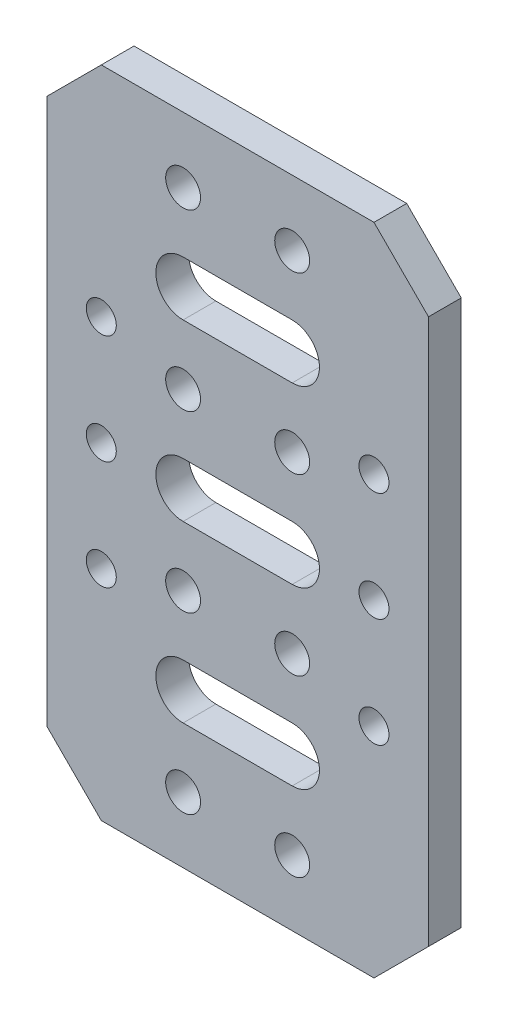
SolidWorks part; units mm, degrees
material "Thornel Mat VMA"
ref_plane "前视基准面" through (0, 0, 0) normal (0, 0, 1) x (1, 0, 0)
ref_plane "上视基准面" through (0, 0, 0) normal (0, 1, 0) x (1, 0, 0)
ref_plane "右视基准面" through (0, 0, 0) normal (1, 0, 0) x (0, 0, -1)
sketch "草图1" plane through (0, 0, 0) normal (0, 0, 1) x (1, 0, 0)
  line L0 (0, 0) -> (-5, 0) construction
  line L1 (-17.5, 30) -> (17.5, 30)
  line L2 (-17.5, 30) -> (-17.5, -30)
  line L3 (-17.5, -30) -> (17.5, -30)
  line L4 (17.5, 30) -> (17.5, -30)
  line L5 (-17.5, 30) -> (17.5, -30) construction
  line L6 (-17.5, -30) -> (17.5, 30) construction
  line L7 (-5, 0) -> (-5, 8) construction
  line L8 (0, 0) -> (0, 6.0639) construction
  circle A0 centre (-5, 8) radius 1.6
  circle A1 centre (5, 8) radius 1.6
  circle A2 centre (-5, 24) radius 1.6
  circle A3 centre (5, 24) radius 1.6
  circle A4 centre (-5, -8) radius 1.6
  circle A5 centre (5, -8) radius 1.6
  circle A6 centre (-5, -24) radius 1.6
  circle A7 centre (5, -24) radius 1.6
  point P0 (0, 0)
  dimension "D5" = 3.2
  dimension "D1" = 35
  dimension "D2" = 60
  dimension "D3" = 5
  dimension "D4" = 8
  dimension "D6" = 2
  dimension "D7" = 3
extrude "凸台-拉伸1" add sketch "草图1" along normal blind 3
sketch "草图2" plane through (0, 0, 3) normal (0, 0, 1) x (1, 0, 0)
  line L0 (0, 0) -> (12.5, 0) construction
  line L1 (0, 0) -> (0, -14.4385) construction
  circle A0 centre (12.5, 0) radius 1.375
  circle A1 centre (-12.5, 0) radius 1.375
  circle A2 centre (-12.5, 10) radius 1.375
  circle A3 centre (12.5, 10) radius 1.375
  circle A4 centre (-12.5, -10) radius 1.375
  circle A5 centre (12.5, -10) radius 1.375
  dimension "D2" = 2.75
  dimension "D1" = 12.5
  dimension "D3" = 2
  dimension "D4" = 2
extrude "切除-拉伸1" cut sketch "草图2" against normal up to next
chamfer "倒角1" distance 5 angle 45 4 edges at (17.5, -30, 1.5) (-17.5, -30, 1.5) (17.5, 30, 1.5) (-17.5, 30, 1.5)
sketch "草图3" plane through (0, 0, 3) normal (0, 0, 1) x (1, 0, 0)
  line L0 (-5, 0) -> (5, 0) construction
  line L1 (-5, 2.5) -> (5, 2.5)
  line L2 (-5, -2.5) -> (5, -2.5)
  line L3 (-5, 16) -> (5, 16) construction
  line L4 (-5, 18.5) -> (5, 18.5)
  line L5 (-5, 13.5) -> (5, 13.5)
  line L6 (-5, 0) -> (5, 0) construction
  line L7 (-5, 2.5) -> (5, 2.5)
  line L8 (-5, -2.5) -> (5, -2.5)
  line L9 (-5, -16) -> (5, -16) construction
  line L10 (-5, -13.5) -> (5, -13.5)
  line L11 (-5, -18.5) -> (5, -18.5)
  arc A0 (-5, 2.5) -> (-5, -2.5) centre (-5, 0) ccw
  arc A1 (5, -2.5) -> (5, 2.5) centre (5, 0) ccw
  arc A2 (-5, 18.5) -> (-5, 13.5) centre (-5, 16) ccw
  arc A3 (5, 13.5) -> (5, 18.5) centre (5, 16) ccw
  arc A4 (-5, 2.5) -> (-5, -2.5) centre (-5, 0) ccw
  arc A5 (5, -2.5) -> (5, 2.5) centre (5, 0) ccw
  arc A6 (-5, -13.5) -> (-5, -18.5) centre (-5, -16) ccw
  arc A7 (5, -18.5) -> (5, -13.5) centre (5, -16) ccw
  point P2 (0, 0)
  point P13 (0, 16)
  point P20 (0, 0)
  point P27 (0, -16)
  dimension "D1" = 2
  dimension "D2" = 2
extrude "切除-拉伸2" cut sketch "草图3" against normal up to next contours L2 A1 L1 A0 | L5 A3 L4 A2 | L11 A7 L10 A6
